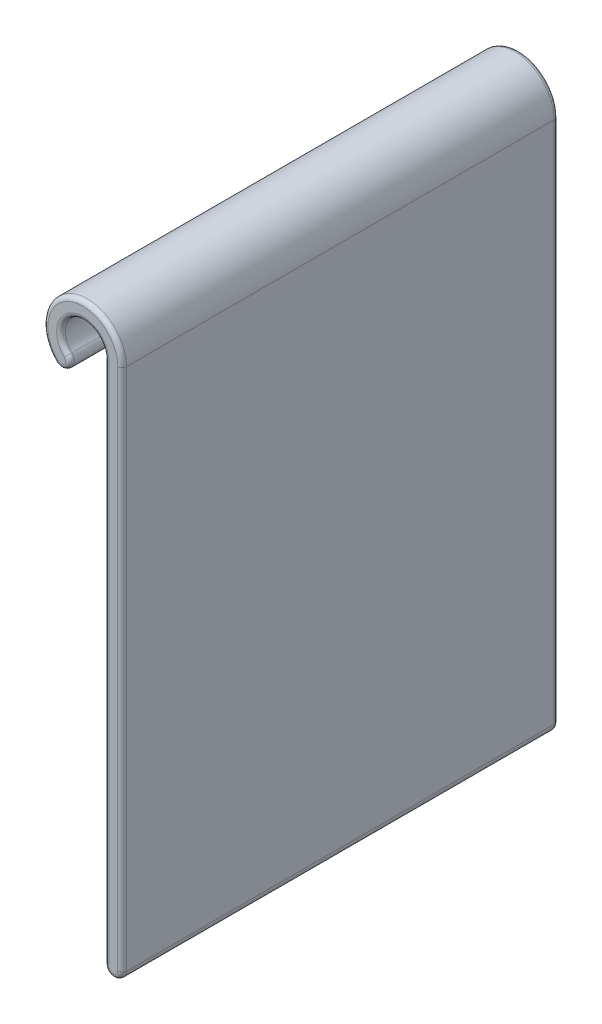
SolidWorks part; units mm, degrees
ref_plane "Front Plane" through (0, 0, 0) normal (0, 0, 1) x (1, 0, 0)
ref_plane "Top Plane" through (0, 0, 0) normal (0, 1, 0) x (1, 0, 0)
ref_plane "Right Plane" through (0, 0, 0) normal (1, 0, 0) x (0, 0, -1)
sketch "Sketch1" plane through (0, 0, 0) normal (0, 0, 1) x (1, 0, 0)
  line L0 (3.175, 0) -> (3.175, -76.2)
  line L1 (5.715, 0) -> (5.715, -76.2)
  line L2 (-2.2451, -2.2451) -> (-4.0411, -4.0411) construction
  line L3 (0, 0) -> (-9.9121, 0) construction
  line L4 (3.175, -76.2) -> (5.715, -76.2) construction
  arc A0 (3.175, 0) -> (-2.2451, -2.2451) centre (0, 0) ccw construction
  arc A1 (3.175, 0) -> (-2.2451, -2.2451) centre (0, 0) ccw
  arc A2 (5.715, 0) -> (-4.0411, -4.0411) centre (0, 0) ccw
  arc A3 (-4.0411, -4.0411) -> (-2.2451, -2.2451) centre (-3.1431, -3.1431) ccw
  arc A4 (3.175, -76.2) -> (5.715, -76.2) centre (4.445, -76.2) ccw
  dimension "D1" = 6.35
  dimension "D2" = 2.54
  dimension "D5" = 1.27
  dimension "D3" = 45
  dimension "D4" = 76.2
extrude "Boss-Extrude1" add sketch "Sketch1" along normal blind 63.5
fillet "Fillet1" radius 0.635 12 edges at (5.715, -38.1, 0) (-2.187, 5.28, 0) (-2.2451, -4.0411, 0) (-1.215, 2.9333, 0) (3.175, -38.1, 0) (4.445, -77.47, 0) (3.175, -38.1, 63.5) (-1.215, 2.9333, 63.5) (-2.2451, -4.0411, 63.5) (-2.187, 5.28, 63.5) (5.715, -38.1, 63.5) (4.445, -77.47, 63.5)
